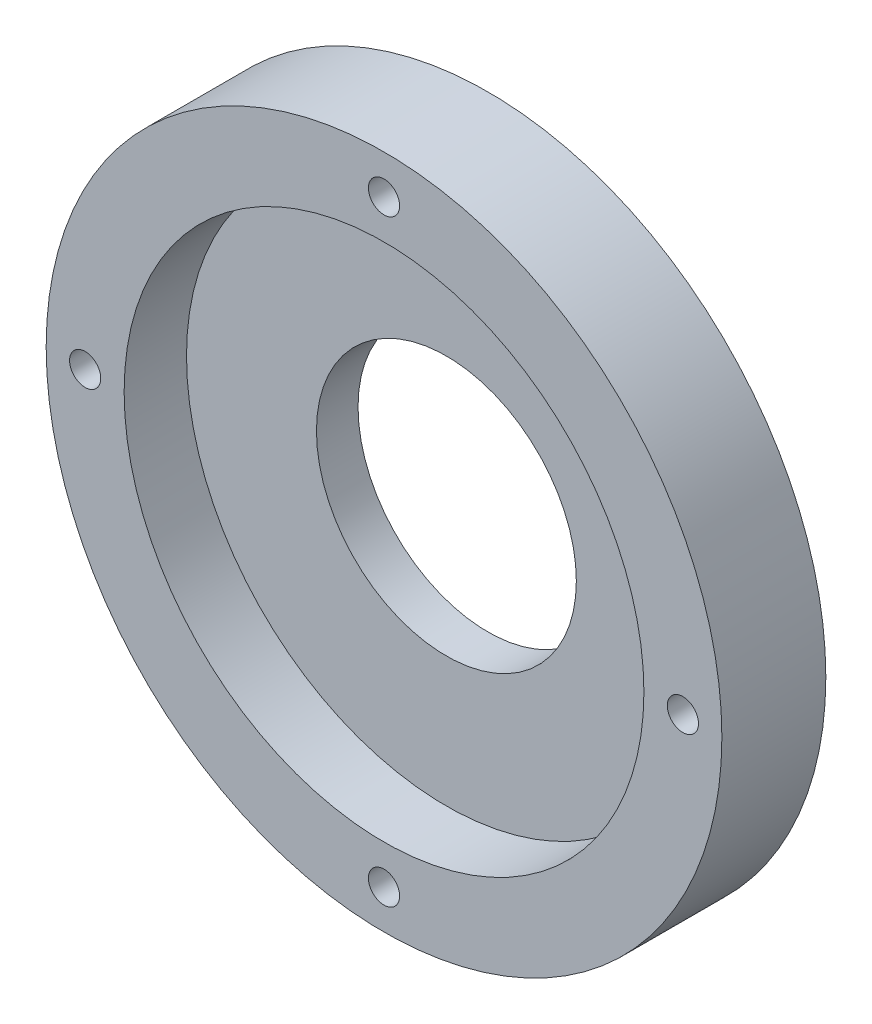
SolidWorks part; units mm, degrees
ref_plane "Plan de face" through (0, 0, 0) normal (0, 0, 1) x (1, 0, 0)
ref_plane "Plan de dessus" through (0, 0, 0) normal (0, 1, 0) x (1, 0, 0)
ref_plane "Plan de droite" through (0, 0, 0) normal (1, 0, 0) x (0, 0, -1)
sketch "Esquisse1" plane through (0, 0, 0) normal (0, 0, 1) x (1, 0, 0)
  circle A0 centre (0, 0) radius 32.5
  dimension "D1" = 65
extrude "Boss.-Extru.1" add sketch "Esquisse1" along normal blind 4
sketch "Esquisse2" plane through (0, 0, 4) normal (0, 0, 1) x (1, 0, 0)
  circle A0 centre (0, 0) radius 25
  circle A1 centre (0, 0) radius 32.5
  dimension "D1" = 50
  dimension "D2" = 65
extrude "Boss.-Extru.2" add sketch "Esquisse2" along normal blind 6
sketch "Esquisse3" plane through (0, 0, 10) normal (0, 0, 1) x (1, 0, 0)
  line L0 (0, 0) -> (0, 32.5) construction
  circle A0 centre (0, 0) radius 32.5 construction
  circle A1 centre (0, 0) radius 25 construction
  circle A2 centre (0, 28.75) radius 1.5
  circle A3 centre (28.75, 0) radius 1.5
  circle A4 centre (0, -28.75) radius 1.5
  circle A5 centre (-28.75, 0) radius 1.5
  point P6 (0, 25)
  point P20 (0, 0)
  dimension "D1" = 3
  dimension "D2" = 3.75
  dimension "D3" = 4
extrude "Enlèv. mat.-Extru.1" cut sketch "Esquisse3" against normal through all
sketch "Esquisse4" plane through (0, 0, 0) normal (0, 0, -1) x (-1, 0, 0)
  circle A0 centre (0, 0) radius 12.5
  dimension "D1" = 25
extrude "Enlèv. mat.-Extru.2" cut sketch "Esquisse4" against normal blind 6
